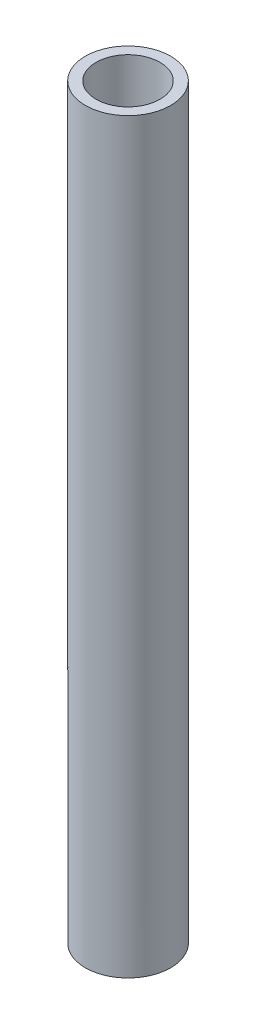
SolidWorks part; units mm, degrees
material "PVC 0.007 Plasticized"
ref_plane "Front Plane" through (0, 0, 0) normal (0, 0, 1) x (1, 0, 0)
ref_plane "Top Plane" through (0, 0, 0) normal (0, 1, 0) x (1, 0, 0)
ref_plane "Right Plane" through (0, 0, 0) normal (1, 0, 0) x (0, 0, -1)
sketch "Sketch1" plane through (0, 0, 0) normal (0, 1, 0) x (1, 0, 0)
  circle A0 centre (0, 0) radius 12.7
  circle A1 centre (0, 0) radius 9.525
  dimension "D1" = 19.05
  dimension "D2" = 25.4
extrude "Boss-Extrude1" add sketch "Sketch1" along normal up to surface (222.25 mm away)
